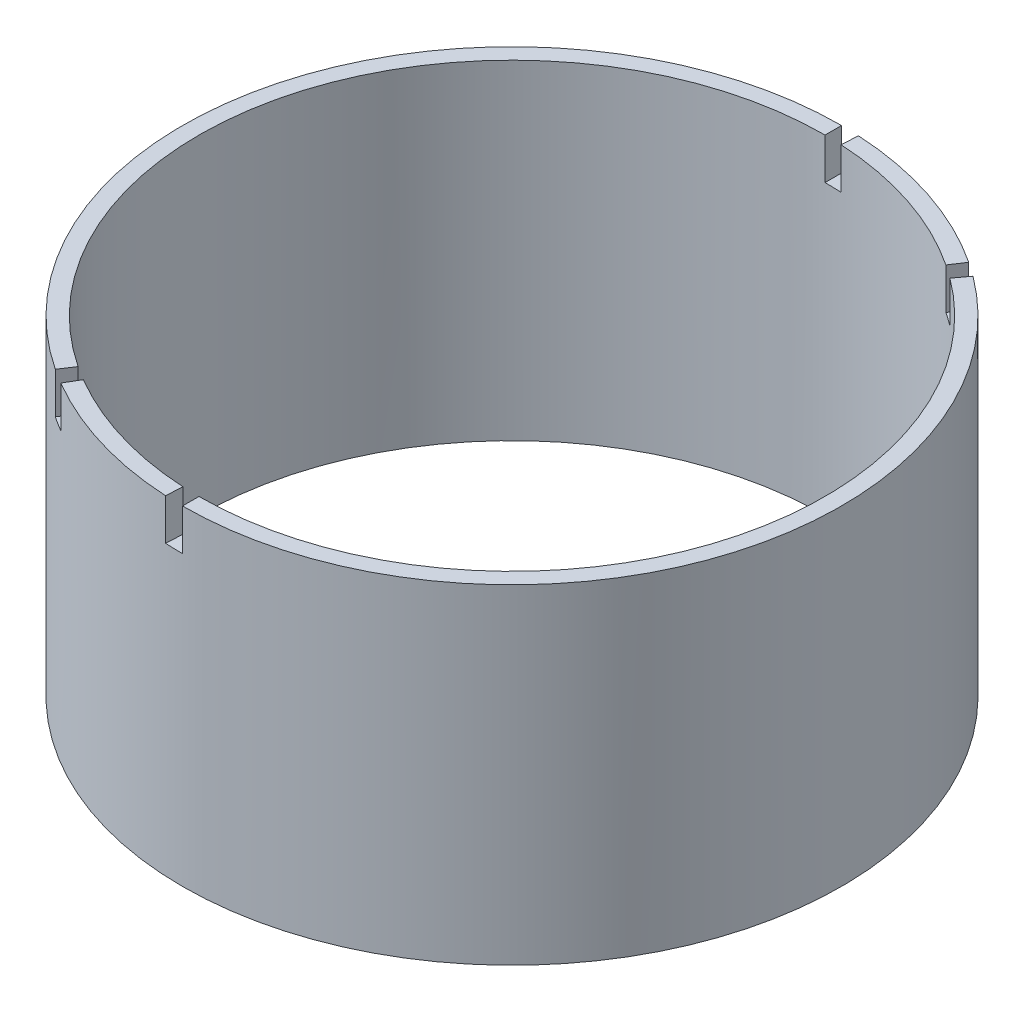
SolidWorks part; units mm, degrees
ref_plane "Plan de face" through (0, 0, 0) normal (0, 0, 1) x (1, 0, 0)
ref_plane "Plan de dessus" through (0, 0, 0) normal (0, 1, 0) x (1, 0, 0)
ref_plane "Plan de droite" through (0, 0, 0) normal (1, 0, 0) x (0, 0, -1)
sketch "Esquisse1" plane through (0, 0, 0) normal (0, 1, 0) x (1, 0, 0)
  circle A0 centre (0, 0) radius 40
  circle A1 centre (0, 0) radius 38
  dimension "D1" = 80
  dimension "D2" = 2
extrude "Extrusion1" add sketch "Esquisse1" along normal blind 40
sketch "Esquisse2" plane through (0, 40, 0) normal (0, 1, 0) x (1, 0, 0)
  line L0 (0, 0) -> (0, 40) construction
  line L1 (0, 0) -> (0, -40) construction
  line L2 (0, -40) -> (0, -38)
  line L3 (0, 40) -> (0, 38)
  line L4 (0, 0) -> (2.1053, 39.9446) construction
  line L5 (0, 0) -> (-2.1053, -39.9446) construction
  line L6 (-2.1053, -39.9446) -> (-2, -37.9473)
  line L7 (2.1053, 39.9446) -> (2, 37.9473)
  line L8 (0, 0) -> (22.0961, 33.3431) construction
  line L9 (22.0961, 33.3431) -> (20.9913, 31.6759)
  line L10 (0, 0) -> (23.8198, 32.1344) construction
  line L11 (23.8198, 32.1344) -> (22.6288, 30.5276)
  line L12 (0, 0) -> (-20.3112, -34.4595) construction
  line L13 (-20.3112, -34.4595) -> (-19.2957, -32.7365)
  line L14 (0, 0) -> (-22.0961, -33.3431) construction
  line L15 (-22.0961, -33.3431) -> (-20.9913, -31.6759)
  circle A0 centre (0, 0) radius 40 construction
  circle A1 centre (0, 0) radius 38 construction
  arc A2 (0, 40) -> (2.1053, 39.9446) centre (0, 0) cw
  arc A3 (0, 38) -> (2, 37.9473) centre (0, 0) cw
  arc A4 (-2, -37.9473) -> (0, -38) centre (0, 0) ccw
  arc A5 (-2.1053, -39.9446) -> (0, -40) centre (0, 0) ccw
  arc A6 (22.0961, 33.3431) -> (23.8198, 32.1344) centre (0, 0) cw
  arc A7 (20.9913, 31.6759) -> (22.6288, 30.5276) centre (0, 0) cw
  circle A8 centre (0, 0) radius 40 construction
  circle A9 centre (0, 0) radius 38 construction
  arc A10 (-20.3112, -34.4595) -> (-22.0961, -33.3431) centre (0, 0) cw
  arc A11 (-19.2957, -32.7365) -> (-20.9913, -31.6759) centre (0, 0) cw
  circle A12 centre (0, 0) radius 40 construction
  circle A13 centre (0, 0) radius 38 construction
  dimension "D1" = 2
  dimension "D2" = 2
  dimension "D3" = 20
  dimension "D4" = 2
extrude "Extrusion2" cut sketch "Esquisse2" against normal blind 5
